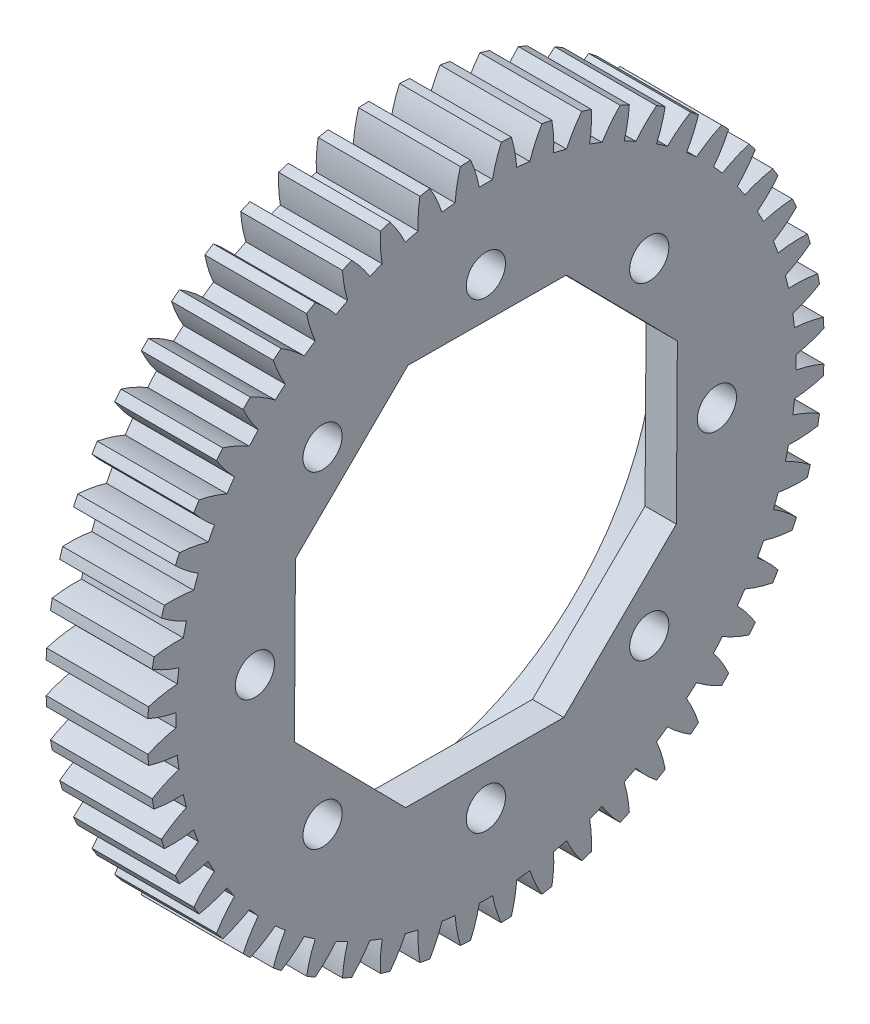
SolidWorks part; units mm, degrees
material "1023 Chapa de acero al carbono (SS)"
ref_plane "Alzado" through (0, 0, 0) normal (0, 0, 1) x (1, 0, 0)
ref_plane "Planta" through (0, 0, 0) normal (0, 1, 0) x (1, 0, 0)
ref_plane "Vista lateral" through (0, 0, 0) normal (1, 0, 0) x (0, 0, -1)
ref_plane "Plano1" through (0, 0, 0) normal (0, 0, -1) x (-1, 0, 0)
sketch "Croquis1" plane through (0, 0, 0) normal (0, 0, -1) x (-1, 0, 0)
  line L0 (-6.5, 21.6) -> (-6.5, 0)
  line L1 (-6.5, 0) -> (0, 0)
  line L2 (0, 0) -> (0, 21.6)
  line L3 (0, 21.6) -> (-6.5, 21.6)
  line L4 (-6.5, 0) -> (0, 0) construction
revolve "Revolución1" add sketch "Croquis1" angle 360 about L4
sketch "Croquis2" plane through (6.5, 0, 0) normal (1, 0, 0) x (0, 0, -1)
  arc A0 (-21.3019, 3.5764) -> (-21.5388, 1.6254) centre (0, 0) ccw
  arc A1 (-21.5388, 1.6254) -> (-19.7012, 1.9655) centre (-19.1154, -6.3339) cw
  arc A2 (-19.7012, 1.9655) -> (-19.5991, 2.8064) centre (0, 0) cw
  arc A3 (-19.5991, 2.8064) -> (-21.3019, 3.5764) centre (-17.0442, 10.7244) cw
extrude "Cortar-Extruir1" cut sketch "Croquis2" against normal through all
sketch "Croquis3" plane through (6.5, 0, 0) normal (1, 0, 0) x (0, 0, -1)
  arc A0 (-20.7155, 6.118) -> (-21.1858, 4.2097) centre (0, 0) ccw
  arc A1 (-21.1858, 4.2097) -> (-19.3206, 4.3259) centre (-19.7395, -3.9836) cw
  arc A2 (-19.3206, 4.3259) -> (-19.1179, 5.1484) centre (0, 0) cw
  arc A3 (-19.1179, 5.1484) -> (-20.7155, 6.118) centre (-15.6272, 12.7007) cw
extrude "Cortar-Extruir2" cut sketch "Croquis3" against normal through all
sketch "Croquis4" plane through (6.5, 0, 0) normal (1, 0, 0) x (0, 0, -1)
  arc A0 (-19.827, 8.5703) -> (-20.5239, 6.7327) centre (0, 0) ccw
  arc A1 (-20.5239, 6.7327) -> (-18.6583, 6.6232) centre (-20.0758, -1.5752) cw
  arc A2 (-18.6583, 6.6232) -> (-18.358, 7.4153) centre (0, 0) cw
  arc A3 (-18.358, 7.4153) -> (-19.827, 8.5703) centre (-13.9824, 14.4918) cw
extrude "Cortar-Extruir3" cut sketch "Croquis4" against normal through all
sketch "Croquis5" plane through (6.5, 0, 0) normal (1, 0, 0) x (0, 0, -1)
  arc A0 (-18.6494, 10.8977) -> (-19.5627, 9.1575) centre (0, 0) ccw
  arc A1 (-19.5627, 9.1575) -> (-17.724, 8.8239) centre (-20.1193, 0.8562) cw
  arc A2 (-17.724, 8.8239) -> (-17.3303, 9.574) centre (0, 0) cw
  arc A3 (-17.3303, 9.574) -> (-18.6494, 10.8977) centre (-12.1336, 16.0715) cw
extrude "Cortar-Extruir4" cut sketch "Croquis5" against normal through all
sketch "Croquis6" plane through (6.5, 0, 0) normal (1, 0, 0) x (0, 0, -1)
  arc A0 (-17.1998, 13.0662) -> (-18.3163, 11.4488) centre (0, 0) ccw
  arc A1 (-18.3163, 11.4488) -> (-16.5311, 10.8959) centre (-19.8694, 3.275) cw
  arc A2 (-16.5311, 10.8959) -> (-16.0499, 11.5931) centre (0, 0) cw
  arc A3 (-16.0499, 11.5931) -> (-17.1998, 13.0662) centre (-10.108, 17.4168) cw
extrude "Cortar-Extruir5" cut sketch "Croquis6" against normal through all
sketch "Croquis7" plane through (6.5, 0, 0) normal (1, 0, 0) x (0, 0, -1)
  arc A0 (-15.4995, 15.0442) -> (-16.8027, 13.5731) centre (0, 0) ccw
  arc A1 (-16.8027, 13.5731) -> (-15.0973, 12.8091) centre (-19.3297, 5.6461) cw
  arc A2 (-15.0973, 12.8091) -> (-14.5355, 13.4432) centre (0, 0) cw
  arc A3 (-14.5355, 13.4432) -> (-15.4995, 15.0442) centre (-7.9349, 18.5082) cw
extrude "Cortar-Extruir6" cut sketch "Croquis7" against normal through all
sketch "Croquis8" plane through (6.5, 0, 0) normal (1, 0, 0) x (0, 0, -1)
  arc A0 (-13.5731, 16.8027) -> (-15.0442, 15.4995) centre (0, 0) ccw
  arc A1 (-15.0442, 15.4995) -> (-13.4432, 14.5355) centre (-18.5082, 7.9349) cw
  arc A2 (-13.4432, 14.5355) -> (-12.8091, 15.0973) centre (0, 0) cw
  arc A3 (-12.8091, 15.0973) -> (-13.5731, 16.8027) centre (-5.6461, 19.3297) cw
extrude "Cortar-Extruir7" cut sketch "Croquis8" against normal through all
sketch "Croquis9" plane through (6.5, 0, 0) normal (1, 0, 0) x (0, 0, -1)
  arc A0 (-11.4488, 18.3163) -> (-13.0662, 17.1998) centre (0, 0) ccw
  arc A1 (-13.0662, 17.1998) -> (-11.5931, 16.0499) centre (-17.4168, 10.108) cw
  arc A2 (-11.5931, 16.0499) -> (-10.8959, 16.5311) centre (0, 0) cw
  arc A3 (-10.8959, 16.5311) -> (-11.4488, 18.3163) centre (-3.275, 19.8694) cw
extrude "Cortar-Extruir8" cut sketch "Croquis9" against normal through all
sketch "Croquis10" plane through (6.5, 0, 0) normal (1, 0, 0) x (0, 0, -1)
  arc A0 (-9.1575, 19.5627) -> (-10.8977, 18.6494) centre (0, 0) ccw
  arc A1 (-10.8977, 18.6494) -> (-9.574, 17.3303) centre (-16.0715, 12.1336) cw
  arc A2 (-9.574, 17.3303) -> (-8.8239, 17.724) centre (0, 0) cw
  arc A3 (-8.8239, 17.724) -> (-9.1575, 19.5627) centre (-0.8562, 20.1193) cw
extrude "Cortar-Extruir9" cut sketch "Croquis10" against normal through all
sketch "Croquis11" plane through (6.5, 0, 0) normal (1, 0, 0) x (0, 0, -1)
  arc A0 (-6.7327, 20.5239) -> (-8.5703, 19.827) centre (0, 0) ccw
  arc A1 (-8.5703, 19.827) -> (-7.4153, 18.358) centre (-14.4918, 13.9824) cw
  arc A2 (-7.4153, 18.358) -> (-6.6232, 18.6583) centre (0, 0) cw
  arc A3 (-6.6232, 18.6583) -> (-6.7327, 20.5239) centre (1.5752, 20.0758) cw
extrude "Cortar-Extruir10" cut sketch "Croquis11" against normal through all
sketch "Croquis12" plane through (6.5, 0, 0) normal (1, 0, 0) x (0, 0, -1)
  arc A0 (-4.2097, 21.1858) -> (-6.118, 20.7155) centre (0, 0) ccw
  arc A1 (-6.118, 20.7155) -> (-5.1484, 19.1179) centre (-12.7007, 15.6272) cw
  arc A2 (-5.1484, 19.1179) -> (-4.3259, 19.3206) centre (0, 0) cw
  arc A3 (-4.3259, 19.3206) -> (-4.2097, 21.1858) centre (3.9836, 19.7395) cw
extrude "Cortar-Extruir11" cut sketch "Croquis12" against normal through all
sketch "Croquis13" plane through (6.5, 0, 0) normal (1, 0, 0) x (0, 0, -1)
  arc A0 (-1.6254, 21.5388) -> (-3.5764, 21.3019) centre (0, 0) ccw
  arc A1 (-3.5764, 21.3019) -> (-2.8064, 19.5991) centre (-10.7244, 17.0442) cw
  arc A2 (-2.8064, 19.5991) -> (-1.9655, 19.7012) centre (0, 0) cw
  arc A3 (-1.9655, 19.7012) -> (-1.6254, 21.5388) centre (6.3339, 19.1154) cw
extrude "Cortar-Extruir12" cut sketch "Croquis13" against normal through all
sketch "Croquis14" plane through (6.5, 0, 0) normal (1, 0, 0) x (0, 0, -1)
  arc A0 (0.9827, 21.5776) -> (-0.9827, 21.5776) centre (0, 0) ccw
  arc A1 (-0.9827, 21.5776) -> (-0.4236, 19.7945) centre (-8.5918, 18.2126) cw
  arc A2 (-0.4236, 19.7945) -> (0.4236, 19.7945) centre (0, 0) cw
  arc A3 (0.4236, 19.7945) -> (0.9827, 21.5776) centre (8.5918, 18.2126) cw
extrude "Cortar-Extruir13" cut sketch "Croquis14" against normal through all
sketch "Croquis15" plane through (6.5, 0, 0) normal (1, 0, 0) x (0, 0, -1)
  arc A0 (3.5764, 21.3019) -> (1.6254, 21.5388) centre (0, 0) ccw
  arc A1 (1.6254, 21.5388) -> (1.9655, 19.7012) centre (-6.3339, 19.1154) cw
  arc A2 (1.9655, 19.7012) -> (2.8064, 19.5991) centre (0, 0) cw
  arc A3 (2.8064, 19.5991) -> (3.5764, 21.3019) centre (10.7244, 17.0442) cw
extrude "Cortar-Extruir14" cut sketch "Croquis15" against normal through all
sketch "Croquis16" plane through (6.5, 0, 0) normal (1, 0, 0) x (0, 0, -1)
  arc A0 (6.118, 20.7155) -> (4.2097, 21.1858) centre (0, 0) ccw
  arc A1 (4.2097, 21.1858) -> (4.3259, 19.3206) centre (-3.9836, 19.7395) cw
  arc A2 (4.3259, 19.3206) -> (5.1484, 19.1179) centre (0, 0) cw
  arc A3 (5.1484, 19.1179) -> (6.118, 20.7155) centre (12.7007, 15.6272) cw
extrude "Cortar-Extruir15" cut sketch "Croquis16" against normal through all
sketch "Croquis17" plane through (6.5, 0, 0) normal (1, 0, 0) x (0, 0, -1)
  arc A0 (8.5703, 19.827) -> (6.7327, 20.5239) centre (0, 0) ccw
  arc A1 (6.7327, 20.5239) -> (6.6232, 18.6583) centre (-1.5752, 20.0758) cw
  arc A2 (6.6232, 18.6583) -> (7.4153, 18.358) centre (0, 0) cw
  arc A3 (7.4153, 18.358) -> (8.5703, 19.827) centre (14.4918, 13.9824) cw
extrude "Cortar-Extruir16" cut sketch "Croquis17" against normal through all
sketch "Croquis18" plane through (6.5, 0, 0) normal (1, 0, 0) x (0, 0, -1)
  arc A0 (10.8977, 18.6494) -> (9.1575, 19.5627) centre (0, 0) ccw
  arc A1 (9.1575, 19.5627) -> (8.8239, 17.724) centre (0.8562, 20.1193) cw
  arc A2 (8.8239, 17.724) -> (9.574, 17.3303) centre (0, 0) cw
  arc A3 (9.574, 17.3303) -> (10.8977, 18.6494) centre (16.0715, 12.1336) cw
extrude "Cortar-Extruir17" cut sketch "Croquis18" against normal through all
sketch "Croquis19" plane through (6.5, 0, 0) normal (1, 0, 0) x (0, 0, -1)
  arc A0 (13.0662, 17.1998) -> (11.4488, 18.3163) centre (0, 0) ccw
  arc A1 (11.4488, 18.3163) -> (10.8959, 16.5311) centre (3.275, 19.8694) cw
  arc A2 (10.8959, 16.5311) -> (11.5931, 16.0499) centre (0, 0) cw
  arc A3 (11.5931, 16.0499) -> (13.0662, 17.1998) centre (17.4168, 10.108) cw
extrude "Cortar-Extruir18" cut sketch "Croquis19" against normal through all
sketch "Croquis20" plane through (6.5, 0, 0) normal (1, 0, 0) x (0, 0, -1)
  arc A0 (15.0442, 15.4995) -> (13.5731, 16.8027) centre (0, 0) ccw
  arc A1 (13.5731, 16.8027) -> (12.8091, 15.0973) centre (5.6461, 19.3297) cw
  arc A2 (12.8091, 15.0973) -> (13.4432, 14.5355) centre (0, 0) cw
  arc A3 (13.4432, 14.5355) -> (15.0442, 15.4995) centre (18.5082, 7.9349) cw
extrude "Cortar-Extruir19" cut sketch "Croquis20" against normal through all
sketch "Croquis21" plane through (6.5, 0, 0) normal (1, 0, 0) x (0, 0, -1)
  arc A0 (16.8027, 13.5731) -> (15.4995, 15.0442) centre (0, 0) ccw
  arc A1 (15.4995, 15.0442) -> (14.5355, 13.4432) centre (7.9349, 18.5082) cw
  arc A2 (14.5355, 13.4432) -> (15.0973, 12.8091) centre (0, 0) cw
  arc A3 (15.0973, 12.8091) -> (16.8027, 13.5731) centre (19.3297, 5.6461) cw
extrude "Cortar-Extruir20" cut sketch "Croquis21" against normal through all
sketch "Croquis22" plane through (6.5, 0, 0) normal (1, 0, 0) x (0, 0, -1)
  arc A0 (18.3163, 11.4488) -> (17.1998, 13.0662) centre (0, 0) ccw
  arc A1 (17.1998, 13.0662) -> (16.0499, 11.5931) centre (10.108, 17.4168) cw
  arc A2 (16.0499, 11.5931) -> (16.5311, 10.8959) centre (0, 0) cw
  arc A3 (16.5311, 10.8959) -> (18.3163, 11.4488) centre (19.8694, 3.275) cw
extrude "Cortar-Extruir21" cut sketch "Croquis22" against normal through all
sketch "Croquis23" plane through (6.5, 0, 0) normal (1, 0, 0) x (0, 0, -1)
  arc A0 (19.5627, 9.1575) -> (18.6494, 10.8977) centre (0, 0) ccw
  arc A1 (18.6494, 10.8977) -> (17.3303, 9.574) centre (12.1336, 16.0715) cw
  arc A2 (17.3303, 9.574) -> (17.724, 8.8239) centre (0, 0) cw
  arc A3 (17.724, 8.8239) -> (19.5627, 9.1575) centre (20.1193, 0.8562) cw
extrude "Cortar-Extruir22" cut sketch "Croquis23" against normal through all
sketch "Croquis24" plane through (6.5, 0, 0) normal (1, 0, 0) x (0, 0, -1)
  arc A0 (20.5239, 6.7327) -> (19.827, 8.5703) centre (0, 0) ccw
  arc A1 (19.827, 8.5703) -> (18.358, 7.4153) centre (13.9824, 14.4918) cw
  arc A2 (18.358, 7.4153) -> (18.6583, 6.6232) centre (0, 0) cw
  arc A3 (18.6583, 6.6232) -> (20.5239, 6.7327) centre (20.0758, -1.5752) cw
extrude "Cortar-Extruir23" cut sketch "Croquis24" against normal through all
sketch "Croquis25" plane through (6.5, 0, 0) normal (1, 0, 0) x (0, 0, -1)
  arc A0 (21.1858, 4.2097) -> (20.7155, 6.118) centre (0, 0) ccw
  arc A1 (20.7155, 6.118) -> (19.1179, 5.1484) centre (15.6272, 12.7007) cw
  arc A2 (19.1179, 5.1484) -> (19.3206, 4.3259) centre (0, 0) cw
  arc A3 (19.3206, 4.3259) -> (21.1858, 4.2097) centre (19.7395, -3.9836) cw
extrude "Cortar-Extruir24" cut sketch "Croquis25" against normal through all
sketch "Croquis26" plane through (6.5, 0, 0) normal (1, 0, 0) x (0, 0, -1)
  arc A0 (21.5388, 1.6254) -> (21.3019, 3.5764) centre (0, 0) ccw
  arc A1 (21.3019, 3.5764) -> (19.5991, 2.8064) centre (17.0442, 10.7244) cw
  arc A2 (19.5991, 2.8064) -> (19.7012, 1.9655) centre (0, 0) cw
  arc A3 (19.7012, 1.9655) -> (21.5388, 1.6254) centre (19.1154, -6.3339) cw
extrude "Cortar-Extruir25" cut sketch "Croquis26" against normal through all
sketch "Croquis27" plane through (6.5, 0, 0) normal (1, 0, 0) x (0, 0, -1)
  arc A0 (21.5776, -0.9827) -> (21.5776, 0.9827) centre (0, 0) ccw
  arc A1 (21.5776, 0.9827) -> (19.7945, 0.4236) centre (18.2126, 8.5918) cw
  arc A2 (19.7945, 0.4236) -> (19.7945, -0.4236) centre (0, 0) cw
  arc A3 (19.7945, -0.4236) -> (21.5776, -0.9827) centre (18.2126, -8.5918) cw
extrude "Cortar-Extruir26" cut sketch "Croquis27" against normal through all
sketch "Croquis28" plane through (6.5, 0, 0) normal (1, 0, 0) x (0, 0, -1)
  arc A0 (21.3019, -3.5764) -> (21.5388, -1.6254) centre (0, 0) ccw
  arc A1 (21.5388, -1.6254) -> (19.7012, -1.9655) centre (19.1154, 6.3339) cw
  arc A2 (19.7012, -1.9655) -> (19.5991, -2.8064) centre (0, 0) cw
  arc A3 (19.5991, -2.8064) -> (21.3019, -3.5764) centre (17.0442, -10.7244) cw
extrude "Cortar-Extruir27" cut sketch "Croquis28" against normal through all
sketch "Croquis29" plane through (6.5, 0, 0) normal (1, 0, 0) x (0, 0, -1)
  arc A0 (20.7155, -6.118) -> (21.1858, -4.2097) centre (0, 0) ccw
  arc A1 (21.1858, -4.2097) -> (19.3206, -4.3259) centre (19.7395, 3.9836) cw
  arc A2 (19.3206, -4.3259) -> (19.1179, -5.1484) centre (0, 0) cw
  arc A3 (19.1179, -5.1484) -> (20.7155, -6.118) centre (15.6272, -12.7007) cw
extrude "Cortar-Extruir28" cut sketch "Croquis29" against normal through all
sketch "Croquis30" plane through (6.5, 0, 0) normal (1, 0, 0) x (0, 0, -1)
  arc A0 (19.827, -8.5703) -> (20.5239, -6.7327) centre (0, 0) ccw
  arc A1 (20.5239, -6.7327) -> (18.6583, -6.6232) centre (20.0758, 1.5752) cw
  arc A2 (18.6583, -6.6232) -> (18.358, -7.4153) centre (0, 0) cw
  arc A3 (18.358, -7.4153) -> (19.827, -8.5703) centre (13.9824, -14.4918) cw
extrude "Cortar-Extruir29" cut sketch "Croquis30" against normal through all
sketch "Croquis31" plane through (6.5, 0, 0) normal (1, 0, 0) x (0, 0, -1)
  arc A0 (18.6494, -10.8977) -> (19.5627, -9.1575) centre (0, 0) ccw
  arc A1 (19.5627, -9.1575) -> (17.724, -8.8239) centre (20.1193, -0.8562) cw
  arc A2 (17.724, -8.8239) -> (17.3303, -9.574) centre (0, 0) cw
  arc A3 (17.3303, -9.574) -> (18.6494, -10.8977) centre (12.1336, -16.0715) cw
extrude "Cortar-Extruir30" cut sketch "Croquis31" against normal through all
sketch "Croquis32" plane through (6.5, 0, 0) normal (1, 0, 0) x (0, 0, -1)
  arc A0 (17.1998, -13.0662) -> (18.3163, -11.4488) centre (0, 0) ccw
  arc A1 (18.3163, -11.4488) -> (16.5311, -10.8959) centre (19.8694, -3.275) cw
  arc A2 (16.5311, -10.8959) -> (16.0499, -11.5931) centre (0, 0) cw
  arc A3 (16.0499, -11.5931) -> (17.1998, -13.0662) centre (10.108, -17.4168) cw
extrude "Cortar-Extruir31" cut sketch "Croquis32" against normal through all
sketch "Croquis33" plane through (6.5, 0, 0) normal (1, 0, 0) x (0, 0, -1)
  arc A0 (15.4995, -15.0442) -> (16.8027, -13.5731) centre (0, 0) ccw
  arc A1 (16.8027, -13.5731) -> (15.0973, -12.8091) centre (19.3297, -5.6461) cw
  arc A2 (15.0973, -12.8091) -> (14.5355, -13.4432) centre (0, 0) cw
  arc A3 (14.5355, -13.4432) -> (15.4995, -15.0442) centre (7.9349, -18.5082) cw
extrude "Cortar-Extruir32" cut sketch "Croquis33" against normal through all
sketch "Croquis34" plane through (6.5, 0, 0) normal (1, 0, 0) x (0, 0, -1)
  arc A0 (13.5731, -16.8027) -> (15.0442, -15.4995) centre (0, 0) ccw
  arc A1 (15.0442, -15.4995) -> (13.4432, -14.5355) centre (18.5082, -7.9349) cw
  arc A2 (13.4432, -14.5355) -> (12.8091, -15.0973) centre (0, 0) cw
  arc A3 (12.8091, -15.0973) -> (13.5731, -16.8027) centre (5.6461, -19.3297) cw
extrude "Cortar-Extruir33" cut sketch "Croquis34" against normal through all
sketch "Croquis35" plane through (6.5, 0, 0) normal (1, 0, 0) x (0, 0, -1)
  arc A0 (11.4488, -18.3163) -> (13.0662, -17.1998) centre (0, 0) ccw
  arc A1 (13.0662, -17.1998) -> (11.5931, -16.0499) centre (17.4168, -10.108) cw
  arc A2 (11.5931, -16.0499) -> (10.8959, -16.5311) centre (0, 0) cw
  arc A3 (10.8959, -16.5311) -> (11.4488, -18.3163) centre (3.275, -19.8694) cw
extrude "Cortar-Extruir34" cut sketch "Croquis35" against normal through all
sketch "Croquis36" plane through (6.5, 0, 0) normal (1, 0, 0) x (0, 0, -1)
  arc A0 (9.1575, -19.5627) -> (10.8977, -18.6494) centre (0, 0) ccw
  arc A1 (10.8977, -18.6494) -> (9.574, -17.3303) centre (16.0715, -12.1336) cw
  arc A2 (9.574, -17.3303) -> (8.8239, -17.724) centre (0, 0) cw
  arc A3 (8.8239, -17.724) -> (9.1575, -19.5627) centre (0.8562, -20.1193) cw
extrude "Cortar-Extruir35" cut sketch "Croquis36" against normal through all
sketch "Croquis37" plane through (6.5, 0, 0) normal (1, 0, 0) x (0, 0, -1)
  arc A0 (6.7327, -20.5239) -> (8.5703, -19.827) centre (0, 0) ccw
  arc A1 (8.5703, -19.827) -> (7.4153, -18.358) centre (14.4918, -13.9824) cw
  arc A2 (7.4153, -18.358) -> (6.6232, -18.6583) centre (0, 0) cw
  arc A3 (6.6232, -18.6583) -> (6.7327, -20.5239) centre (-1.5752, -20.0758) cw
extrude "Cortar-Extruir36" cut sketch "Croquis37" against normal through all
sketch "Croquis38" plane through (6.5, 0, 0) normal (1, 0, 0) x (0, 0, -1)
  arc A0 (4.2097, -21.1858) -> (6.118, -20.7155) centre (0, 0) ccw
  arc A1 (6.118, -20.7155) -> (5.1484, -19.1179) centre (12.7007, -15.6272) cw
  arc A2 (5.1484, -19.1179) -> (4.3259, -19.3206) centre (0, 0) cw
  arc A3 (4.3259, -19.3206) -> (4.2097, -21.1858) centre (-3.9836, -19.7395) cw
extrude "Cortar-Extruir37" cut sketch "Croquis38" against normal through all
sketch "Croquis39" plane through (6.5, 0, 0) normal (1, 0, 0) x (0, 0, -1)
  arc A0 (1.6254, -21.5388) -> (3.5764, -21.3019) centre (0, 0) ccw
  arc A1 (3.5764, -21.3019) -> (2.8064, -19.5991) centre (10.7244, -17.0442) cw
  arc A2 (2.8064, -19.5991) -> (1.9655, -19.7012) centre (0, 0) cw
  arc A3 (1.9655, -19.7012) -> (1.6254, -21.5388) centre (-6.3339, -19.1154) cw
extrude "Cortar-Extruir38" cut sketch "Croquis39" against normal through all
sketch "Croquis40" plane through (6.5, 0, 0) normal (1, 0, 0) x (0, 0, -1)
  arc A0 (-0.9827, -21.5776) -> (0.9827, -21.5776) centre (0, 0) ccw
  arc A1 (0.9827, -21.5776) -> (0.4236, -19.7945) centre (8.5918, -18.2126) cw
  arc A2 (0.4236, -19.7945) -> (-0.4236, -19.7945) centre (0, 0) cw
  arc A3 (-0.4236, -19.7945) -> (-0.9827, -21.5776) centre (-8.5918, -18.2126) cw
extrude "Cortar-Extruir39" cut sketch "Croquis40" against normal through all
sketch "Croquis41" plane through (6.5, 0, 0) normal (1, 0, 0) x (0, 0, -1)
  arc A0 (-3.5764, -21.3019) -> (-1.6254, -21.5388) centre (0, 0) ccw
  arc A1 (-1.6254, -21.5388) -> (-1.9655, -19.7012) centre (6.3339, -19.1154) cw
  arc A2 (-1.9655, -19.7012) -> (-2.8064, -19.5991) centre (0, 0) cw
  arc A3 (-2.8064, -19.5991) -> (-3.5764, -21.3019) centre (-10.7244, -17.0442) cw
extrude "Cortar-Extruir40" cut sketch "Croquis41" against normal through all
sketch "Croquis42" plane through (6.5, 0, 0) normal (1, 0, 0) x (0, 0, -1)
  arc A0 (-6.118, -20.7155) -> (-4.2097, -21.1858) centre (0, 0) ccw
  arc A1 (-4.2097, -21.1858) -> (-4.3259, -19.3206) centre (3.9836, -19.7395) cw
  arc A2 (-4.3259, -19.3206) -> (-5.1484, -19.1179) centre (0, 0) cw
  arc A3 (-5.1484, -19.1179) -> (-6.118, -20.7155) centre (-12.7007, -15.6272) cw
extrude "Cortar-Extruir41" cut sketch "Croquis42" against normal through all
sketch "Croquis43" plane through (6.5, 0, 0) normal (1, 0, 0) x (0, 0, -1)
  arc A0 (-8.5703, -19.827) -> (-6.7327, -20.5239) centre (0, 0) ccw
  arc A1 (-6.7327, -20.5239) -> (-6.6232, -18.6583) centre (1.5752, -20.0758) cw
  arc A2 (-6.6232, -18.6583) -> (-7.4153, -18.358) centre (0, 0) cw
  arc A3 (-7.4153, -18.358) -> (-8.5703, -19.827) centre (-14.4918, -13.9824) cw
extrude "Cortar-Extruir42" cut sketch "Croquis43" against normal through all
sketch "Croquis44" plane through (6.5, 0, 0) normal (1, 0, 0) x (0, 0, -1)
  arc A0 (-10.8977, -18.6494) -> (-9.1575, -19.5627) centre (0, 0) ccw
  arc A1 (-9.1575, -19.5627) -> (-8.8239, -17.724) centre (-0.8562, -20.1193) cw
  arc A2 (-8.8239, -17.724) -> (-9.574, -17.3303) centre (0, 0) cw
  arc A3 (-9.574, -17.3303) -> (-10.8977, -18.6494) centre (-16.0715, -12.1336) cw
extrude "Cortar-Extruir43" cut sketch "Croquis44" against normal through all
sketch "Croquis45" plane through (6.5, 0, 0) normal (1, 0, 0) x (0, 0, -1)
  arc A0 (-13.0662, -17.1998) -> (-11.4488, -18.3163) centre (0, 0) ccw
  arc A1 (-11.4488, -18.3163) -> (-10.8959, -16.5311) centre (-3.275, -19.8694) cw
  arc A2 (-10.8959, -16.5311) -> (-11.5931, -16.0499) centre (0, 0) cw
  arc A3 (-11.5931, -16.0499) -> (-13.0662, -17.1998) centre (-17.4168, -10.108) cw
extrude "Cortar-Extruir44" cut sketch "Croquis45" against normal through all
sketch "Croquis46" plane through (6.5, 0, 0) normal (1, 0, 0) x (0, 0, -1)
  arc A0 (-15.0442, -15.4995) -> (-13.5731, -16.8027) centre (0, 0) ccw
  arc A1 (-13.5731, -16.8027) -> (-12.8091, -15.0973) centre (-5.6461, -19.3297) cw
  arc A2 (-12.8091, -15.0973) -> (-13.4432, -14.5355) centre (0, 0) cw
  arc A3 (-13.4432, -14.5355) -> (-15.0442, -15.4995) centre (-18.5082, -7.9349) cw
extrude "Cortar-Extruir45" cut sketch "Croquis46" against normal through all
sketch "Croquis47" plane through (6.5, 0, 0) normal (1, 0, 0) x (0, 0, -1)
  arc A0 (-16.8027, -13.5731) -> (-15.4995, -15.0442) centre (0, 0) ccw
  arc A1 (-15.4995, -15.0442) -> (-14.5355, -13.4432) centre (-7.9349, -18.5082) cw
  arc A2 (-14.5355, -13.4432) -> (-15.0973, -12.8091) centre (0, 0) cw
  arc A3 (-15.0973, -12.8091) -> (-16.8027, -13.5731) centre (-19.3297, -5.6461) cw
extrude "Cortar-Extruir46" cut sketch "Croquis47" against normal through all
sketch "Croquis48" plane through (6.5, 0, 0) normal (1, 0, 0) x (0, 0, -1)
  arc A0 (-18.3163, -11.4488) -> (-17.1998, -13.0662) centre (0, 0) ccw
  arc A1 (-17.1998, -13.0662) -> (-16.0499, -11.5931) centre (-10.108, -17.4168) cw
  arc A2 (-16.0499, -11.5931) -> (-16.5311, -10.8959) centre (0, 0) cw
  arc A3 (-16.5311, -10.8959) -> (-18.3163, -11.4488) centre (-19.8694, -3.275) cw
extrude "Cortar-Extruir47" cut sketch "Croquis48" against normal through all
sketch "Croquis49" plane through (6.5, 0, 0) normal (1, 0, 0) x (0, 0, -1)
  arc A0 (-19.5627, -9.1575) -> (-18.6494, -10.8977) centre (0, 0) ccw
  arc A1 (-18.6494, -10.8977) -> (-17.3303, -9.574) centre (-12.1336, -16.0715) cw
  arc A2 (-17.3303, -9.574) -> (-17.724, -8.8239) centre (0, 0) cw
  arc A3 (-17.724, -8.8239) -> (-19.5627, -9.1575) centre (-20.1193, -0.8562) cw
extrude "Cortar-Extruir48" cut sketch "Croquis49" against normal through all
sketch "Croquis50" plane through (6.5, 0, 0) normal (1, 0, 0) x (0, 0, -1)
  arc A0 (-20.5239, -6.7327) -> (-19.827, -8.5703) centre (0, 0) ccw
  arc A1 (-19.827, -8.5703) -> (-18.358, -7.4153) centre (-13.9824, -14.4918) cw
  arc A2 (-18.358, -7.4153) -> (-18.6583, -6.6232) centre (0, 0) cw
  arc A3 (-18.6583, -6.6232) -> (-20.5239, -6.7327) centre (-20.0758, 1.5752) cw
extrude "Cortar-Extruir49" cut sketch "Croquis50" against normal through all
sketch "Croquis51" plane through (6.5, 0, 0) normal (1, 0, 0) x (0, 0, -1)
  arc A0 (-21.1858, -4.2097) -> (-20.7155, -6.118) centre (0, 0) ccw
  arc A1 (-20.7155, -6.118) -> (-19.1179, -5.1484) centre (-15.6272, -12.7007) cw
  arc A2 (-19.1179, -5.1484) -> (-19.3206, -4.3259) centre (0, 0) cw
  arc A3 (-19.3206, -4.3259) -> (-21.1858, -4.2097) centre (-19.7395, 3.9836) cw
extrude "Cortar-Extruir50" cut sketch "Croquis51" against normal through all
sketch "Croquis52" plane through (6.5, 0, 0) normal (1, 0, 0) x (0, 0, -1)
  arc A0 (-21.5388, -1.6254) -> (-21.3019, -3.5764) centre (0, 0) ccw
  arc A1 (-21.3019, -3.5764) -> (-19.5991, -2.8064) centre (-17.0442, -10.7244) cw
  arc A2 (-19.5991, -2.8064) -> (-19.7012, -1.9655) centre (0, 0) cw
  arc A3 (-19.7012, -1.9655) -> (-21.5388, -1.6254) centre (-19.1154, 6.3339) cw
extrude "Cortar-Extruir51" cut sketch "Croquis52" against normal through all
sketch "Croquis53" plane through (6.5, 0, 0) normal (1, 0, 0) x (0, 0, -1)
  arc A0 (-21.5776, 0.9827) -> (-21.5776, -0.9827) centre (0, 0) ccw
  arc A1 (-21.5776, -0.9827) -> (-19.7945, -0.4236) centre (-18.2126, -8.5918) cw
  arc A2 (-19.7945, -0.4236) -> (-19.7945, 0.4236) centre (0, 0) cw
  arc A3 (-19.7945, 0.4236) -> (-21.5776, 0.9827) centre (-18.2126, 8.5918) cw
extrude "Cortar-Extruir52" cut sketch "Croquis53" against normal through all
hole_wizard "Refrentado para tornillo de fijación de #61" positions "Croquis55" profile "Croquis54" counterbore size "#6" standard "Ansi Inch"
sketch "Croquis55" plane through (0, 0, 0) normal (-1, 0, 0) x (0, 0, 1)
  point P0 (0, 0)
sketch "Croquis54" plane through (0, 0, 0) normal (0, 1, 0) x (0, 0, 1)
  line L0 (0, 0) -> (0, 6.5)
  line L1 (0, 6.5) -> (2, 6.5)
  line L3 (2, 6.5) -> (2, 4.5)
  line L4 (2, 4.5) -> (17.3, 4.5)
  line L5 (17.3, 4.5) -> (17.3, 0)
  line L7 (17.3, 0) -> (0, 0)
  line L11 (0, -6.35) -> (0, 107.95) construction
  dimension "Diámetro de taladro hasta el siguiente" = 4
  dimension "Profundidad de taladro hasta el siguiente" = 6.5
  dimension "Diámetro de refrentado" = 34.6
  dimension "Profundidad de refrentado" = 4.5
hole_wizard "Taladro de margen para #21" positions "Croquis57" profile "Croquis56" hole size "#2" standard "Ansi Inch"
sketch "Croquis57" plane through (6.5, 0, 0) normal (1, 0, 0) x (0, 0, -1)
  point P0 (14.75, 0)
  point P1 (10.4298, -10.4298)
  point P2 (0, -14.75)
  point P3 (-10.4298, -10.4298)
  point P4 (-14.75, 0)
  point P5 (-10.4298, 10.4298)
  point P6 (0, 14.75)
  point P7 (10.4298, 10.4298)
sketch "Croquis56" plane through (6.5, 0, -14.75) normal (0, 1, 0) x (0, 0, -1)
  line L0 (0, 0) -> (0, 6.5)
  line L1 (0, 6.5) -> (1.25, 6.5)
  line L2 (1.25, 6.5) -> (1.25, 0)
  line L5 (1.25, 0) -> (0, 0)
  line L11 (0, -6.35) -> (0, 107.95) construction
  dimension "Diámetro de taladro hasta el siguiente" = 2.5
  dimension "Profundidad de taladro hasta el siguiente" = 6.5
sketch "Croquis58" plane through (6.5, 0, 0) normal (1, 0, 0) x (0, 0, -1)
  line L1 (12.2234, 4.9737) -> (5.1263, 12.1601)
  line L2 (5.1263, 12.1601) -> (-4.9737, 12.2234)
  line L3 (-4.9737, 12.2234) -> (-12.1601, 5.1263)
  line L4 (-12.1601, 5.1263) -> (-12.2234, -4.9737)
  line L5 (-12.2234, -4.9737) -> (-5.1263, -12.1601)
  line L6 (-5.1263, -12.1601) -> (4.9737, -12.2234)
  line L7 (4.9737, -12.2234) -> (12.1601, -5.1263)
  line L8 (12.1601, -5.1263) -> (12.2234, 4.9737)
  circle A0 centre (0, 0) radius 12.192 construction
  dimension "D1" = 24.384
extrude "Cortar-Extruir54" cut sketch "Croquis58" against normal blind 2.54 contours L1 L2 L3 L4 L5 L6 L7 L8
